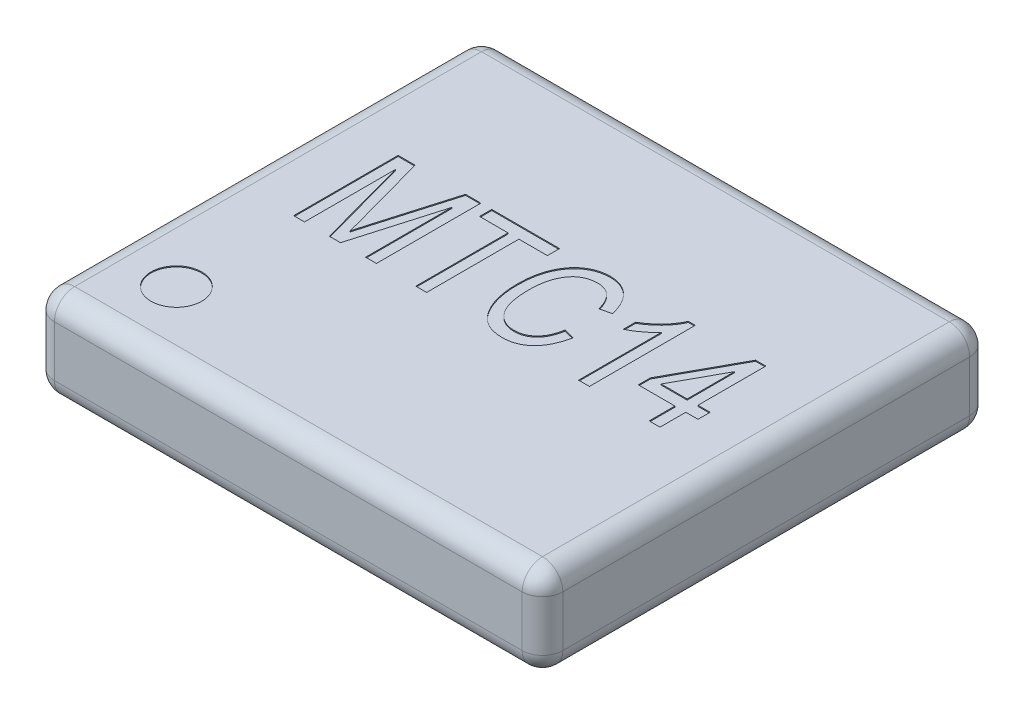
SolidWorks part; units mm, degrees
ref_plane "Front Plane" through (0, 0, 0) normal (0, 0, 1) x (1, 0, 0)
ref_plane "Top Plane" through (0, 0, 0) normal (0, 1, 0) x (1, 0, 0)
ref_plane "Right Plane" through (0, 0, 0) normal (1, 0, 0) x (0, 0, -1)
sketch "Sketch1" plane through (0, 0, 0) normal (0, 1, 0) x (1, 0, 0)
  line L1 (-2.5, -2.2) -> (2.5, -2.2)
  line L2 (-2.5, -2.2) -> (-2.5, 2.2)
  line L3 (-2.5, 2.2) -> (2.5, 2.2)
  line L4 (2.5, -2.2) -> (2.5, 2.2)
  line L5 (-2.5, -2.2) -> (2.5, 2.2) construction
  line L6 (-2.5, 2.2) -> (2.5, -2.2) construction
  point P0 (0, 0)
  dimension "D1" = 5
  dimension "D2" = 4.4
extrude "Boss-Extrude1" add sketch "Sketch1" along normal mid plane 0.9
fillet "Fillet1" radius 0.2 12 edges at (2.5, 0, 2.2) (-2.5, 0, 2.2) (2.5, 0, -2.2) (-2.5, 0, -2.2) (-2.5, -0.45, 0) (0, -0.45, -2.2) (2.5, -0.45, 0) (0, -0.45, 2.2) (0, 0.45, -2.2) (2.5, 0.45, 0) (0, 0.45, 2.2) (-2.5, 0.45, 0)
sketch "Sketch2" plane through (0, 0.45, 0) normal (0, 1, 0) x (1, 0, 0)
  line L0 (-2.3, -2) -> (2.3, -2) construction
  line L1 (-2.3, 2) -> (-2.3, -2) construction
  circle A0 centre (-1.8, -1.5) radius 0.25
  dimension "D3" = 0.5
  dimension "D1" = 0.5
  dimension "D2" = 0.5
extrude "Cut-Extrude1" cut sketch "Sketch2" against normal blind 0.01
sketch "Sketch3" plane through (0, 0.45, 0) normal (0, 1, 0) x (1, 0, 0)
  line L0 (-1.9207, -0.3197) -> (1.9862, -0.3197) construction
  text T0 "MTC14\r\n" font "Arial Narrow" height in points 4
  point P3 (1.9862, -0.3504)
  point P4 (-2.102, -0.3547)
  point P5 (-1.9207, -0.638)
extrude "Cut-Extrude2" cut sketch "Sketch3" against normal blind 0.01
